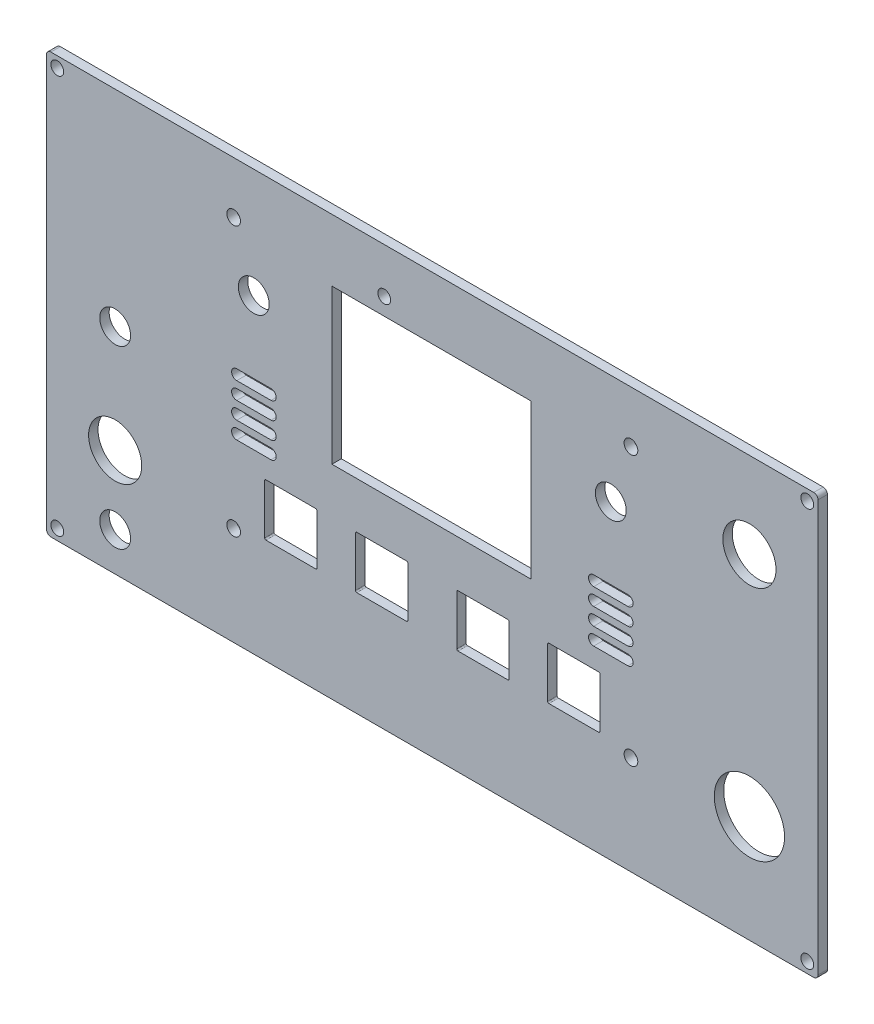
SolidWorks part; units mm, degrees
ref_plane "Спереди" through (0, 0, 0) normal (0, 0, 1) x (1, 0, 0)
ref_plane "Сверху" through (0, 0, 0) normal (0, 1, 0) x (1, 0, 0)
ref_plane "Справа" through (0, 0, 0) normal (1, 0, 0) x (0, 0, -1)
sketch "Эскиз1" plane through (0, 0, 0) normal (0, 0, 1) x (1, 0, 0)
  line L0 (3.556, 69.977) -> (3.556, 0) construction
  line L1 (0, 0) -> (99.822, 0) construction
  line L2 (0, 0) -> (0, 69.977) construction
  line L3 (0, 69.977) -> (99.822, 69.977) construction
  line L4 (99.822, 0) -> (99.822, 69.977) construction
  line L5 (96.266, 69.977) -> (96.266, 0) construction
  line L6 (0, 66.421) -> (99.822, 66.421) construction
  line L7 (0, 3.556) -> (99.822, 3.556) construction
  line L8 (49.911, 69.977) -> (49.911, 0) construction
  line L9 (0, 34.9885) -> (99.822, 34.9885) construction
  line L10 (-40.089, 5.5) -> (139.911, 5.5) construction
  line L11 (-40.089, 78.5) -> (139.911, 78.5)
  line L12 (-40.089, 78.5) -> (-40.089, -19.5)
  line L13 (-40.089, -19.5) -> (139.911, -19.5)
  line L14 (139.911, 78.5) -> (139.911, -19.5)
  line L15 (-40.089, 78.5) -> (139.911, -19.5) construction
  line L16 (-40.089, -19.5) -> (139.911, 78.5) construction
  line L17 (-40.089, 58.5) -> (139.911, 58.5) construction
  line L18 (-24.089, 78.5) -> (-24.089, -19.5) construction
  line L19 (123.911, 78.5) -> (123.911, -19.5) construction
  line L20 (-37.589, 78.5) -> (-37.589, -20.4429) construction
  line L21 (137.411, 78.5) -> (137.411, -19.5) construction
  line L22 (-40.089, 76) -> (139.911, 76) construction
  line L23 (-40.089, -17) -> (139.911, -17) construction
  line L24 (0, 52.959) -> (99.822, 52.959) construction
  line L25 (0, 11.049) -> (99.822, 11.049) construction
  line L26 (8.255, 69.977) -> (8.255, 0) construction
  line L27 (91.567, 69.977) -> (91.567, 0) construction
  line L28 (16.891, 0) -> (16.891, 11.049) construction
  line L29 (38.1, 0) -> (38.1, 11.049) construction
  line L30 (61.722, 0) -> (61.722, 11.049) construction
  line L31 (82.931, 0) -> (82.931, 11.049) construction
  line L32 (4.283, 34.9885) -> (12.283, 34.9885) construction
  line L33 (10.791, 17.149) -> (22.991, 17.149)
  line L34 (10.791, 17.149) -> (10.791, 4.949)
  line L35 (10.791, 4.949) -> (22.991, 4.949)
  line L36 (22.991, 17.149) -> (22.991, 4.949)
  line L37 (10.791, 17.149) -> (22.991, 4.949) construction
  line L38 (10.791, 4.949) -> (22.991, 17.149) construction
  line L39 (32, 17.149) -> (44.2, 17.149)
  line L40 (32, 17.149) -> (32, 4.949)
  line L41 (32, 4.949) -> (44.2, 4.949)
  line L42 (44.2, 17.149) -> (44.2, 4.949)
  line L43 (32, 17.149) -> (44.2, 4.949) construction
  line L44 (32, 4.949) -> (44.2, 17.149) construction
  line L45 (55.622, 17.149) -> (67.822, 17.149)
  line L46 (55.622, 17.149) -> (55.622, 4.949)
  line L47 (55.622, 4.949) -> (67.822, 4.949)
  line L48 (67.822, 17.149) -> (67.822, 4.949)
  line L49 (55.622, 17.149) -> (67.822, 4.949) construction
  line L50 (55.622, 4.949) -> (67.822, 17.149) construction
  line L51 (76.831, 17.149) -> (89.031, 17.149)
  line L52 (76.831, 17.149) -> (76.831, 4.949)
  line L53 (76.831, 4.949) -> (89.031, 4.949)
  line L54 (89.031, 17.149) -> (89.031, 4.949)
  line L55 (76.831, 17.149) -> (89.031, 4.949) construction
  line L56 (76.831, 4.949) -> (89.031, 17.149) construction
  line L57 (26.5, 28) -> (73, 28)
  line L58 (26.5, 28) -> (26.5, 64)
  line L59 (26.5, 64) -> (73, 64)
  line L60 (73, 28) -> (73, 64)
  line L61 (4.283, 36.1885) -> (12.283, 36.1885)
  line L62 (4.283, 33.7885) -> (12.283, 33.7885)
  line L63 (95.567, 34.9885) -> (87.567, 34.9885) construction
  line L64 (95.567, 33.7885) -> (87.567, 33.7885)
  line L65 (95.567, 36.1885) -> (87.567, 36.1885)
  line L66 (4.283, 30.9885) -> (12.283, 30.9885) construction
  line L67 (4.283, 32.1885) -> (12.283, 32.1885)
  line L68 (4.283, 29.7885) -> (12.283, 29.7885)
  line L69 (95.567, 30.9885) -> (87.567, 30.9885) construction
  line L70 (95.567, 29.7885) -> (87.567, 29.7885)
  line L71 (95.567, 32.1885) -> (87.567, 32.1885)
  line L72 (4.283, 26.9885) -> (12.283, 26.9885) construction
  line L73 (4.283, 28.1885) -> (12.283, 28.1885)
  line L74 (4.283, 25.7885) -> (12.283, 25.7885)
  line L75 (95.567, 26.9885) -> (87.567, 26.9885) construction
  line L76 (95.567, 25.7885) -> (87.567, 25.7885)
  line L77 (95.567, 28.1885) -> (87.567, 28.1885)
  line L78 (4.283, 22.9885) -> (12.283, 22.9885) construction
  line L79 (4.283, 24.1885) -> (12.283, 24.1885)
  line L80 (4.283, 21.7885) -> (12.283, 21.7885)
  line L81 (95.567, 22.9885) -> (87.567, 22.9885) construction
  line L82 (95.567, 21.7885) -> (87.567, 21.7885)
  line L83 (95.567, 24.1885) -> (87.567, 24.1885)
  circle A0 centre (-24.089, 5.5) radius 6.2
  circle A2 centre (123.911, 58.5) radius 6.2
  circle A3 centre (123.911, 5.5) radius 8.2
  circle A4 centre (-37.589, 76) radius 1.5
  circle A5 centre (137.411, 76) radius 1.5
  circle A6 centre (137.411, -17) radius 1.5
  circle A7 centre (-37.589, -17) radius 1.5
  circle A8 centre (3.556, 3.556) radius 1.6
  circle A9 centre (3.556, 66.421) radius 1.6
  circle A10 centre (96.266, 66.421) radius 1.6
  circle A11 centre (96.266, 3.556) radius 1.6
  circle A12 centre (8.255, 52.959) radius 3.6
  circle A13 centre (91.567, 52.959) radius 3.6
  circle A14 centre (-24.089, 30.5) radius 3.6
  circle A15 centre (-24.089, -10.5) radius 3.6
  arc A16 (4.283, 36.1885) -> (4.283, 33.7885) centre (4.283, 34.9885) ccw
  arc A17 (12.283, 33.7885) -> (12.283, 36.1885) centre (12.283, 34.9885) ccw
  arc A18 (95.567, 33.7885) -> (95.567, 36.1885) centre (95.567, 34.9885) ccw
  arc A19 (87.567, 36.1885) -> (87.567, 33.7885) centre (87.567, 34.9885) ccw
  arc A20 (4.283, 32.1885) -> (4.283, 29.7885) centre (4.283, 30.9885) ccw
  arc A21 (12.283, 29.7885) -> (12.283, 32.1885) centre (12.283, 30.9885) ccw
  arc A22 (95.567, 29.7885) -> (95.567, 32.1885) centre (95.567, 30.9885) ccw
  arc A23 (87.567, 32.1885) -> (87.567, 29.7885) centre (87.567, 30.9885) ccw
  arc A24 (4.283, 28.1885) -> (4.283, 25.7885) centre (4.283, 26.9885) ccw
  arc A25 (12.283, 25.7885) -> (12.283, 28.1885) centre (12.283, 26.9885) ccw
  arc A26 (95.567, 25.7885) -> (95.567, 28.1885) centre (95.567, 26.9885) ccw
  arc A27 (87.567, 28.1885) -> (87.567, 25.7885) centre (87.567, 26.9885) ccw
  arc A28 (4.283, 24.1885) -> (4.283, 21.7885) centre (4.283, 22.9885) ccw
  arc A29 (12.283, 21.7885) -> (12.283, 24.1885) centre (12.283, 22.9885) ccw
  arc A30 (95.567, 21.7885) -> (95.567, 24.1885) centre (95.567, 22.9885) ccw
  arc A31 (87.567, 24.1885) -> (87.567, 21.7885) centre (87.567, 22.9885) ccw
  circle A32 centre (38.7, 68) radius 1.5
  point P17 (49.911, 34.9885)
  point P105 (8.283, 34.9885)
  point P113 (91.567, 34.9885)
  point P120 (8.283, 30.9885)
  point P128 (91.567, 30.9885)
  point P134 (8.283, 26.9885)
  point P142 (91.567, 26.9885)
  point P148 (8.283, 22.9885)
  point P156 (91.567, 22.9885)
  dimension "D13" = 12.4
  dimension "D14" = 16.4
  dimension "D15" = 12.4
  dimension "D16" = 7.2
  dimension "D21" = 3
  dimension "D22" = 3
  dimension "D23" = 3
  dimension "D24" = 3
  dimension "D25" = 3.2
  dimension "D26" = 3.2
  dimension "D27" = 3.2
  dimension "D28" = 3.2
  dimension "D33" = 7.2
  dimension "D34" = 7.2
  dimension "D53" = 7.2
  dimension "D63" = 3
  dimension "D1" = 99.822
  dimension "D2" = 69.977
  dimension "D3" = 3.556
  dimension "D4" = 3.556
  dimension "D5" = 3.556
  dimension "D6" = 3.556
  dimension "D7" = 98
  dimension "D8" = 180
  dimension "D9" = 25
  dimension "D10" = 20
  dimension "D11" = 16
  dimension "D12" = 16
  dimension "D17" = 2.5
  dimension "D18" = 2.5
  dimension "D19" = 2.5
  dimension "D20" = 2.5
  dimension "D29" = 52.959
  dimension "D30" = 11.049
  dimension "D31" = 8.255
  dimension "D32" = 91.567
  dimension "D35" = 16.891
  dimension "D36" = 38.1
  dimension "D37" = 61.722
  dimension "D38" = 82.931
  dimension "D39" = 12.2
  dimension "D40" = 12.2
  dimension "D41" = 12.2
  dimension "D42" = 12.2
  dimension "D43" = 12.2
  dimension "D44" = 12.2
  dimension "D45" = 12.2
  dimension "D46" = 12.2
  dimension "D47" = 17
  dimension "D48" = 6.023
  dimension "D49" = 26.5
  dimension "D50" = 28
  dimension "D51" = 73
  dimension "D52" = 64
  dimension "D54" = 16
  dimension "D55" = 25
  dimension "D56" = 8
  dimension "D57" = 2.4
  dimension "D58" = 8
  dimension "D59" = 2.4
  dimension "D61" = 38.7
  dimension "D62" = 68
  dimension "D60" = 4
extrude "Бобышка-Вытянуть1" add sketch "Эскиз1" along normal blind 2.2
fillet "Скругление1" radius 1 4 edges at (139.911, -19.5, 1.1) (-40.089, -19.5, 1.1) (-40.089, 78.5, 1.1) (139.911, 78.5, 1.1)
fillet "Скругление2" radius 0.3 16 edges at (89.031, 4.949, 1.1) (89.031, 17.149, 1.1) (76.831, 17.149, 1.1) (76.831, 4.949, 1.1) (67.822, 4.949, 1.1) (67.822, 17.149, 1.1) (55.622, 17.149, 1.1) (55.622, 4.949, 1.1) (44.2, 4.949, 1.1) (44.2, 17.149, 1.1) (32, 17.149, 1.1) (32, 4.949, 1.1) (10.791, 4.949, 1.1) (22.991, 4.949, 1.1) (22.991, 17.149, 1.1) (10.791, 17.149, 1.1)
